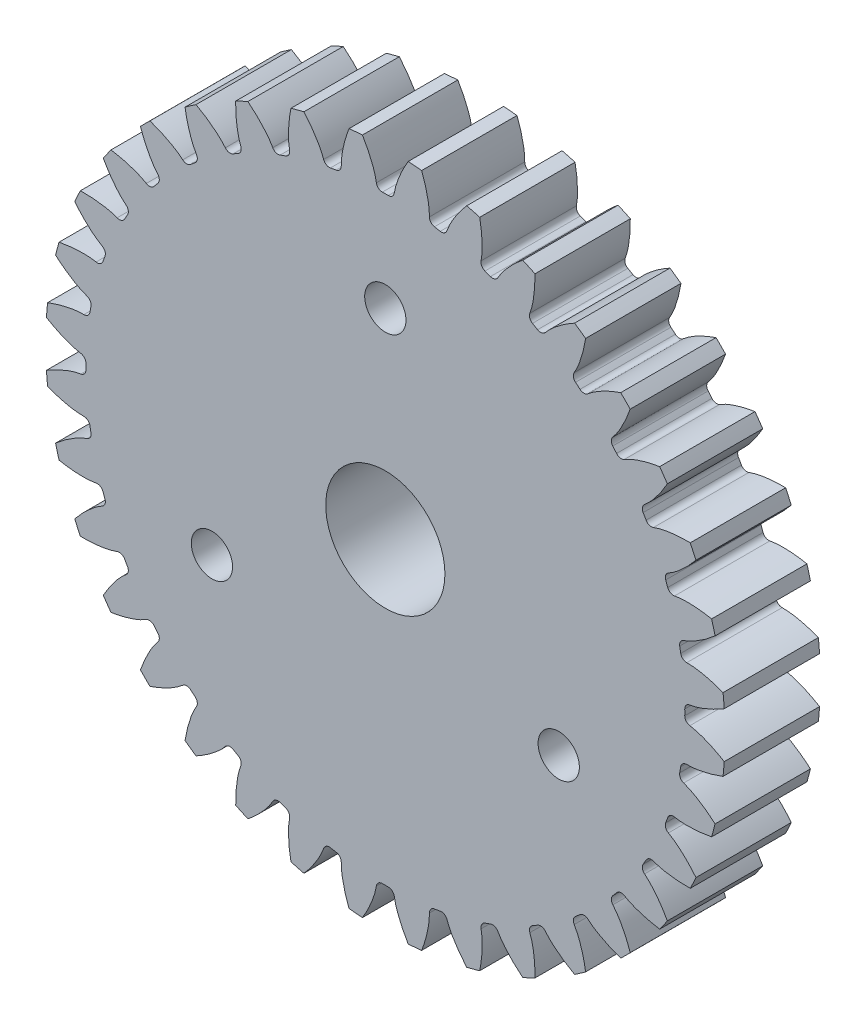
SolidWorks part; units mm, degrees
ref_plane "Front Plane" through (0, 0, 0) normal (0, 0, 1) x (1, 0, 0)
ref_plane "Top Plane" through (0, 0, 0) normal (0, 1, 0) x (1, 0, 0)
ref_plane "Right Plane" through (0, 0, 0) normal (1, 0, 0) x (0, 0, -1)
sketch "Sketch1" plane through (0, 0, 0) normal (0, 0, 1) x (1, 0, 0)
  line L0 (0, 0) -> (0, 14.2875) construction
  line L1 (-4.5919, 15.9588) -> (4.5919, 12.6162) construction
  circle A0 centre (0, 0) radius 13.2953 construction
  circle A1 centre (0, 0) radius 15.0813 construction
  circle A2 centre (0, 0) radius 14.2875 construction
  circle A3 centre (0, 0) radius 13.4259 construction
  circle A4 centre (0, 0) radius 2.6458 construction
  circle A5 centre (0, 0) radius 9.144 construction
  point P8 (406.4, 0)
  point P13 (457.2, 0)
  dimension "OD | Outside Diameter" = 30.1625
  dimension "Root Diameter" = 26.5906
  dimension "Gear Pitch Diameter" = 28.575
  dimension "Base Diameter" = 26.8517
  dimension "For Shaft Diameter" = 5.2917
  dimension "Hub Diameter" = 18.288
  dimension "Pressure Angle" = 20
  dimension "Number of Teeth" = 914.4
  dimension "Gear Pitch | Diametral Pitch" = 812.8
sketch "Sketch2" plane through (0, 0, 0) normal (1, 0, 0) x (0, 0, -1)
  line L0 (-5.5626, 0) -> (5.5626, 0) construction
  line L1 (-5.5626, 15.0813) -> (5.5626, 15.0813) construction
  point P2 (0, 15.0813)
  point P4 (0.7874, 0)
  point P6 (0.7874, 15.0813)
  dimension "Overall Width" = 11.1252
  dimension "Hub Width" = 6.35
  dimension "Face Width" = 4.7752
sketch "Sketch3" plane through (0, 0, 0) normal (0, 0, 1) x (1, 0, 0)
  circle A0 centre (0, 0) radius 15.0813
  circle A1 centre (0, 0) radius 15.0813 construction
extrude "Boss-Extrude1" add sketch "Sketch3" against normal blind 2.1167 and the other way blind 2.1167
sketch "Sketch5" plane through (0, 0, 0) normal (1, 0, 0) x (0, 0, -1)
  line L11 (5.5626, 2.6458) -> (-5.5626, 2.6458)
  line L12 (5.5626, 2.6458) -> (5.5626, 0)
  line L13 (5.5626, 0) -> (-5.5626, 0)
  line L14 (-5.5626, 2.6458) -> (-5.5626, 0)
  point P5 (0, 2.6458)
revolve "Cut-Revolve1" cut sketch "Sketch5" angle 360 about L0
fillet "Fillet2" [suppressed] radius 0.2663
sketch "Sketch4" plane through (0, 0, 0) normal (0, 0, 1) x (1, 0, 0)
  line L0 (0, 0) -> (13.2898, 0.3819) construction
  line L2 (0, 0) -> (13.2898, -0.3819) construction
  line L4 (13.2898, 0.3819) -> (13.4203, 0.3857)
  line L5 (13.4203, -0.3857) -> (13.2898, -0.3819)
  arc A0 (13.2898, 0.3819) -> (13.2898, -0.3819) centre (0, 0) cw
  arc A3 (15.0469, 1.0166) -> (15.0469, -1.0166) centre (0, 0) cw
  circle A4 centre (0, 0) radius 15.0813 construction
  spline S0 degree 4 poles (13.4203, 0.3857) (13.4229, 0.3858) (13.4302, 0.3861) (13.4439, 0.3872) (13.4664, 0.3894) (13.4949, 0.3929) (13.5317, 0.3983) (13.5751, 0.4057) (13.6226, 0.415) (13.6743, 0.4262) (13.7257, 0.4385) (13.777, 0.4518) (13.8279, 0.4659) (13.8896, 0.484) (13.9633, 0.5072) (14.0493, 0.5364) (14.1466, 0.572) (14.2454, 0.611) (14.3424, 0.6516) (14.4401, 0.6952) (14.5343, 0.7391) (14.6319, 0.7873) (14.7218, 0.8331) (14.822, 0.8873) (14.9028, 0.9319) (15.0089, 0.9937) (15.0715, 1.0311) (15.1445, 1.076) (15.1768, 1.0964) (15.1967, 1.109) knots 0 0 0 0 0 0.005377 0.015084 0.028532 0.04661 0.064855 0.092111 0.119476 0.146842 0.174209 0.201575 0.228941 0.256307 0.307035 0.361767 0.4165 0.471232 0.525964 0.580697 0.635429 0.690161 0.744894 0.799626 0.854358 0.909091 0.954545 1 1 1 1 1 construction
  spline S1 degree 4 poles (13.4203, 0.3857) (13.4229, 0.3858) (13.4302, 0.3861) (13.4439, 0.3872) (13.4664, 0.3894) (13.4949, 0.3929) (13.5317, 0.3983) (13.5751, 0.4057) (13.6226, 0.415) (13.6743, 0.4262) (13.7257, 0.4385) (13.777, 0.4518) (13.8279, 0.4659) (13.8896, 0.484) (13.9633, 0.5072) (14.0493, 0.5364) (14.1466, 0.572) (14.2454, 0.611) (14.3424, 0.6516) (14.4401, 0.6952) (14.5343, 0.7391) (14.6319, 0.7873) (14.7218, 0.8331) (14.822, 0.8873) (14.9028, 0.9319) (14.9859, 0.9803) (15.0263, 1.0042) (15.0469, 1.0166) knots 0 0 0 0 0 0.005377 0.015084 0.028532 0.04661 0.064855 0.092111 0.119476 0.146842 0.174209 0.201575 0.228941 0.256307 0.307035 0.361767 0.4165 0.471232 0.525964 0.580697 0.635429 0.690161 0.744894 0.799626 0.854358 0.909091 0.909091 0.909091 0.909091 0.909091
  spline S2 degree 4 poles (13.4203, -0.3857) (13.4229, -0.3858) (13.4302, -0.3861) (13.4439, -0.3872) (13.4664, -0.3894) (13.4949, -0.3929) (13.5317, -0.3983) (13.5751, -0.4057) (13.6226, -0.415) (13.6743, -0.4262) (13.7257, -0.4385) (13.777, -0.4518) (13.8279, -0.4659) (13.8896, -0.484) (13.9633, -0.5072) (14.0493, -0.5364) (14.1466, -0.572) (14.2454, -0.611) (14.3424, -0.6516) (14.4401, -0.6952) (14.5343, -0.7391) (14.6319, -0.7873) (14.7218, -0.8331) (14.822, -0.8873) (14.9028, -0.9319) (15.0089, -0.9937) (15.0715, -1.0311) (15.1445, -1.076) (15.1768, -1.0964) (15.1967, -1.109) knots 0 0 0 0 0 0.005377 0.015084 0.028532 0.04661 0.064855 0.092111 0.119476 0.146842 0.174209 0.201575 0.228941 0.256307 0.307035 0.361767 0.4165 0.471232 0.525964 0.580697 0.635429 0.690161 0.744894 0.799626 0.854358 0.909091 0.954545 1 1 1 1 1 construction
  spline S3 degree 4 poles (13.4203, -0.3857) (13.4229, -0.3858) (13.4302, -0.3861) (13.4439, -0.3872) (13.4664, -0.3894) (13.4949, -0.3929) (13.5317, -0.3983) (13.5751, -0.4057) (13.6226, -0.415) (13.6743, -0.4262) (13.7257, -0.4385) (13.777, -0.4518) (13.8279, -0.4659) (13.8896, -0.484) (13.9633, -0.5072) (14.0493, -0.5364) (14.1466, -0.572) (14.2454, -0.611) (14.3424, -0.6516) (14.4401, -0.6952) (14.5343, -0.7391) (14.6319, -0.7873) (14.7218, -0.8331) (14.822, -0.8873) (14.9028, -0.9319) (14.9859, -0.9803) (15.0263, -1.0042) (15.0469, -1.0166) knots 0 0 0 0 0 0.005377 0.015084 0.028532 0.04661 0.064855 0.092111 0.119476 0.146842 0.174209 0.201575 0.228941 0.256307 0.307035 0.361767 0.4165 0.471232 0.525964 0.580697 0.635429 0.690161 0.744894 0.799626 0.854358 0.909091 0.909091 0.909091 0.909091 0.909091
  dimension "D1" = 26.5906
extrude "Cut-Extrude1" cut sketch "Sketch4" against normal through all both and the other way through all
fillet "Fillet1" radius 0.2663 2 edges at (13.2898, -0.3819, 0) (13.2898, 0.3819, 0)
pattern_circular "CirPattern1" count 36 over 360 about axis through (0, 0, 5.5626) along (0, 0, -1) of "Cut-Extrude1", "Fillet1"
sketch "Sketch6" plane through (0, 0, 2.1167) normal (0, 0, 1) x (1, 0, 0)
  circle A0 centre (0, 0) radius 6.9596
extrude "Cut-Extrude2" [suppressed] cut sketch "Sketch6" against normal blind 1.27
scale "Scale1" scale about centroid uniform scaling yes scale factor 1.2
sketch "Sketch7" plane through (0, 0, 2.54) normal (0, 0, 1) x (1, 0, 0)
  point P3 (0, 10.668)
  point P4 (9.2388, -5.334)
  point P5 (-9.2388, -5.334)
  point P8 (0, 0)
  dimension "D1" = 10.668
  dimension "D2" = 3
hole_wizard "M2 Clearance Hole1" positions "3DSketch4" profile "Sketch11" hole size "M2" standard "ANSI Metric" end condition through all
sketch3d "3DSketch4"
  point P0 (0, 10.668, 2.54)
  point P3 (-9.2388, -5.334, 2.54)
  point P6 (9.2388, -5.334, 2.54)
sketch "Sketch11" plane through (0, 10.668, 2.54) normal (1, 0, 0) x (0, -1, 0)
  line L0 (0, 0) -> (0, 5.08)
  line L1 (0, 5.08) -> (1.1, 5.08)
  line L2 (1.1, 5.08) -> (1.1, 0)
  line L5 (1.1, 0) -> (0, 0)
  line L11 (0, -6.35) -> (0, 107.95) construction
  dimension "Thru Hole Dia." = 2.2
  dimension "Thru Hole Depth" = 5.08
equation "\"Root Diameter@Sketch1\"=\"Root Diameter\""
equation "\"OD | Outside Diameter@Sketch1\"=\"Outside Diameter\""
equation "\"D1@CirPattern1\"=\"Number of Teeth\""
equation "\"Diametral Pitch\"=32"
equation "\"Number of Teeth\"= 36"
equation "\"Pressure Angle\"=20"
equation "\"Pitch Diameter\"= \"Number of Teeth\" / \"Diametral Pitch\""
equation "\"Base Diameter\"= \"Pitch Diameter\" * cos ( \"Pressure Angle\" )"
equation "\"Outside Diameter\"= ( \"Number of Teeth\" + 2 ) / \"Diametral Pitch\""
equation "\"Dedendum\"= 1.25 / \"Diametral Pitch\""
equation "\"Root Diameter\"= \"Pitch Diameter\" - ( 2 * \"Dedendum\" )"
equation "\"Pitch Angle\"= 360deg / \"Number of Teeth\""
equation "\"Alpha\"= sqr ( \"Pitch Diameter\" ^ 2 - \"Base Diameter\" ^ 2 ) / \"Base Diameter\" * 180 / PI - \"Pressure Angle\""
equation "\"Beta\"= ( \"Pitch Angle\" / 4 - \"Alpha\" )"
equation "\"Phi\"= sqr ( ( \"Outside Diameter\" / 2 ) ^ 2 - ( \"Base Diameter\" / 2 ) ^ 2 ) / ( \"Base Diameter\" / 2 )"
equation "\"Addendum\"= 1 / \"Diametral Pitch\""
equation "\"WorkingDepth\"= 2 / \"Diametral Pitch\""
equation "\"WholeDepth\"= 2.25 / \"Diametral Pitch\""
equation "\"Clearance\"= 0.25 / \"Diametral Pitch\""
equation "\"ToothThickness\"= ( pi * 2 ) / \"Diametral Pitch\""
equation "\"CircularPitch\"= pi / \"Diametral Pitch\""
equation "\"Number of Teeth@Sketch1\"=\"Number of Teeth\""
equation "\"Gear Pitch | Diametral Pitch@Sketch1\"=\"Diametral Pitch\""
equation "\"Pressure Angle@Sketch1\"=\"Pressure Angle\""
equation "\"Gear Pitch Diameter@Sketch1\"=\"Pitch Diameter\""
equation "\"Base Diameter@Sketch1\"=\"Base Diameter\""
equation "\"Fillet\"= \"Clearance\" * cos ( \"Pressure Angle\" ) * tan ( ( 90 + \"Pressure Angle\" ) / 2 )"
equation "\"D1@Fillet1\"=\"Fillet\""
equation "\"D1@Sketch4\"=if( \"Base Diameter\">\"Root Diameter\",\"Root Diameter\",\"Base Diameter\"-.00001)"
equation "\"D1@Fillet2\"=\"Fillet\""
